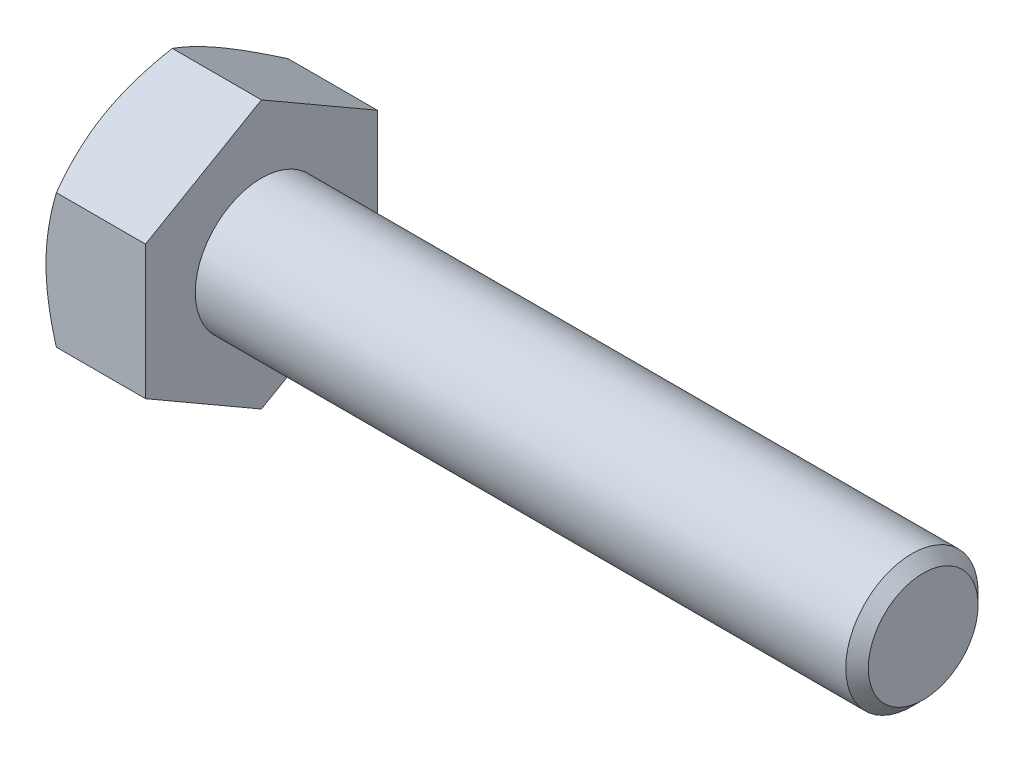
SolidWorks part; units mm, degrees
extrude "BaseHead" add sketch "Sketch1" along normal blind 4.7752
sketch "Sketch1" plane through (0, 0, 0) normal (1, 0, 0) x (0, 0, -1)
  line L0 (5.5626, 3.2116) -> (5.5626, -3.2116)
  line L1 (-5.5626, 3.2116) -> (-5.5626, -3.2116)
  line L2 (5.5626, -3.2116) -> (0, -6.4231)
  line L3 (0, -6.4231) -> (-5.5626, -3.2116)
  line L4 (5.5626, 3.2116) -> (0, 6.4231)
  line L5 (0, 6.4231) -> (-5.5626, 3.2116)
  dimension "Width_flats" = 11.1252
  dimension "D2" = 120
  dimension "D3" = 5.5626
  dimension "D4" = 5.5626
  dimension "D5" = 5.5626
ref_plane "Plane1" through (0, 0, 0) normal (0, 0, 1) x (1, 0, 0)
ref_plane "Plane2" through (0, 0, 0) normal (0, 1, 0) x (1, 0, 0)
ref_plane "Plane3" through (0, 0, 0) normal (1, 0, 0) x (0, 0, -1)
other "Configuration Table"
sketch "BodySke" plane through (0, 0, 0) normal (0, 0, 1) x (1, 0, 0)
  line L0 (0, 3.2116) -> (0, -3.2116) construction
  line L1 (0, 0) -> (36.5252, 0)
  line L2 (0, 0) -> (0, 3.175)
  line L3 (0, 3.175) -> (35.9842, 3.175)
  line L4 (36.5252, 0) -> (36.5252, 2.634)
  line L5 (4.7752, 6.4231) -> (4.7752, 3.2116) construction
  line L6 (36.5252, 2.634) -> (35.9842, 3.175)
  line L7 (0, 0) -> (96.52, 0) construction
  line L8 (36.5252, -2.634) -> (35.9842, -3.175) construction
  line L9 (0, -3.175) -> (35.9842, -3.175) construction
  line L10 (5.682, 15.24) -> (5.682, -2.54) construction
  line L11 (17.4752, 15.24) -> (17.4752, -2.54) construction
  line L12 (4.7752, 3.2116) -> (4.7752, -3.2116) construction
  dimension "Diameter" = 6.35
revolve "BaseBody" add sketch "BodySke" angle 360 about L7
cosmetic thread "ThreadCosmetic" parameters "Thread_length"=19.05, "Thread_minor"=5.268
sketch "Sketch3" plane through (0, 0, 0) normal (0, 0, 1) x (1, 0, 0)
  line L0 (0, 5.5626) -> (4.163, 12.7731)
  line L1 (0, 6.4231) -> (0, 3.2116) construction
  line L2 (4.163, 12.7731) -> (4.163, 19.1231)
  line L3 (4.163, 19.1231) -> (-12.7, 19.1231)
  line L4 (-12.7, 19.1231) -> (-12.7, 5.5626)
  line L5 (-12.7, 5.5626) -> (0, 5.5626)
  line L6 (0, 0) -> (99.06, 0) construction
  line L7 (4.7752, 6.4231) -> (0, 6.4231) construction
  dimension "D1" = 5.5626
  dimension "D2" = 6.35
  dimension "D3" = 12.7
  dimension "D4" = 6.35
  dimension "Head_ch_ang" = 30
revolve "HeadChamfer" cut sketch "Sketch3" angle 360 about L6
fillet "HeadFillet" [suppressed] radius 0.762
sketch "ThdSchSke" plane through (0, 0, 0) normal (0, 0, 1) x (1, 0, 0)
  line L0 (17.4752, -2.634) -> (17.0964, -3.175)
  line L1 (17.4752, -2.634) -> (17.854, -3.175)
  line L2 (17.854, -3.175) -> (17.854, -3.9687)
  line L3 (-3.175, 0) -> (5.1513, 0) construction
  line L5 (17.854, -3.9687) -> (17.0964, -3.9687)
  line L6 (17.0964, -3.9687) -> (17.0964, -3.175)
  dimension "Thread_minor" = 5.268
  dimension "Diameter" = 6.35
  dimension "Start" = 17.4752
revolve "ThreadSchematic" [suppressed] cut sketch "ThdSchSke" angle 360 about L3
pattern_linear "ThdSchPat" [suppressed]
equation "\"D3@Sketch1\" = \"Width_flats@Sketch1\" / 2"
equation "\"D4@Sketch1\" = \"D3@Sketch1\""
equation "\"D5@Sketch1\" = \"D4@Sketch1\""
equation "\"Thread_minor@ThreadCosmetic\" = \"Minor_dia@BodySke\""
equation "\"D1@Sketch3\" = \"Width_flats@Sketch1\" / 2"
equation "\"Thread_length@ThreadCosmetic\" = ((sgn( (\"Length@BodySke\" - \"Advance@BodySke\" ) - \"Thread_nom@BodySke\" )-1)*( (\"Length@BodySke\" - \"Advance@BodySke\" ) - \"Thread_nom@BodySke\" ))/-2+ \"Thread_nom@BodySke\""
equation "\"Thread_minor@ThdSchSke\" = \"Minor_dia@BodySke\""
equation "\"Diameter@ThdSchSke\" = \"Diameter@BodySke\""
equation "\"Overcut@ThdSchSke\" = \"Diameter@BodySke\" * 1.25"
equation "\"Start@ThdSchSke\" = \"Head_ht@BaseHead\" + \"Length@BodySke\" - \"Thread_length@ThreadCosmetic\"  '---Non-countersunk---"
equation "\"Num_threads@ThdSchPat\" = int( \"Thread_length@ThreadCosmetic\" / \"Advance@BodySke\" + 0.999 )  + 1"
equation "\"Advance@ThdSchPat\" = \"Thread_length@ThreadCosmetic\" /  (\"Num_threads@ThdSchPat\" - 1) 'relax it"
equation "\"Num_threads@ThdSchPat\" = \"Num_threads@ThdSchPat\" - sgn( \"Num_threads@ThdSchPat\" - 1) '---chamfered tips only---"
